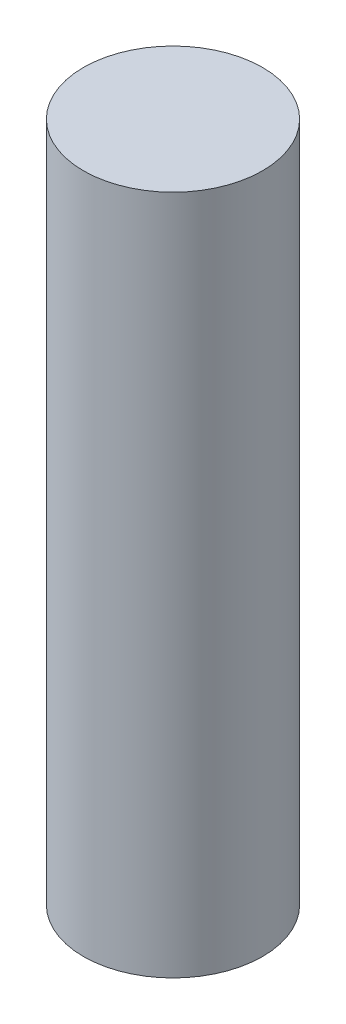
SolidWorks part; units mm, degrees
material "1060 Alloy"
ref_plane "Front Plane" through (0, 0, 0) normal (0, 0, 1) x (1, 0, 0)
ref_plane "Top Plane" through (0, 0, 0) normal (0, 1, 0) x (1, 0, 0)
ref_plane "Right Plane" through (0, 0, 0) normal (1, 0, 0) x (0, 0, -1)
sketch "Sketch1" plane through (0, 0, 0) normal (0, 1, 0) x (1, 0, 0)
  circle A0 centre (0, 0) radius 12.7
  dimension "D1" = 25.4
extrude "Boss-Extrude1" add sketch "Sketch1" along normal blind 96.52
